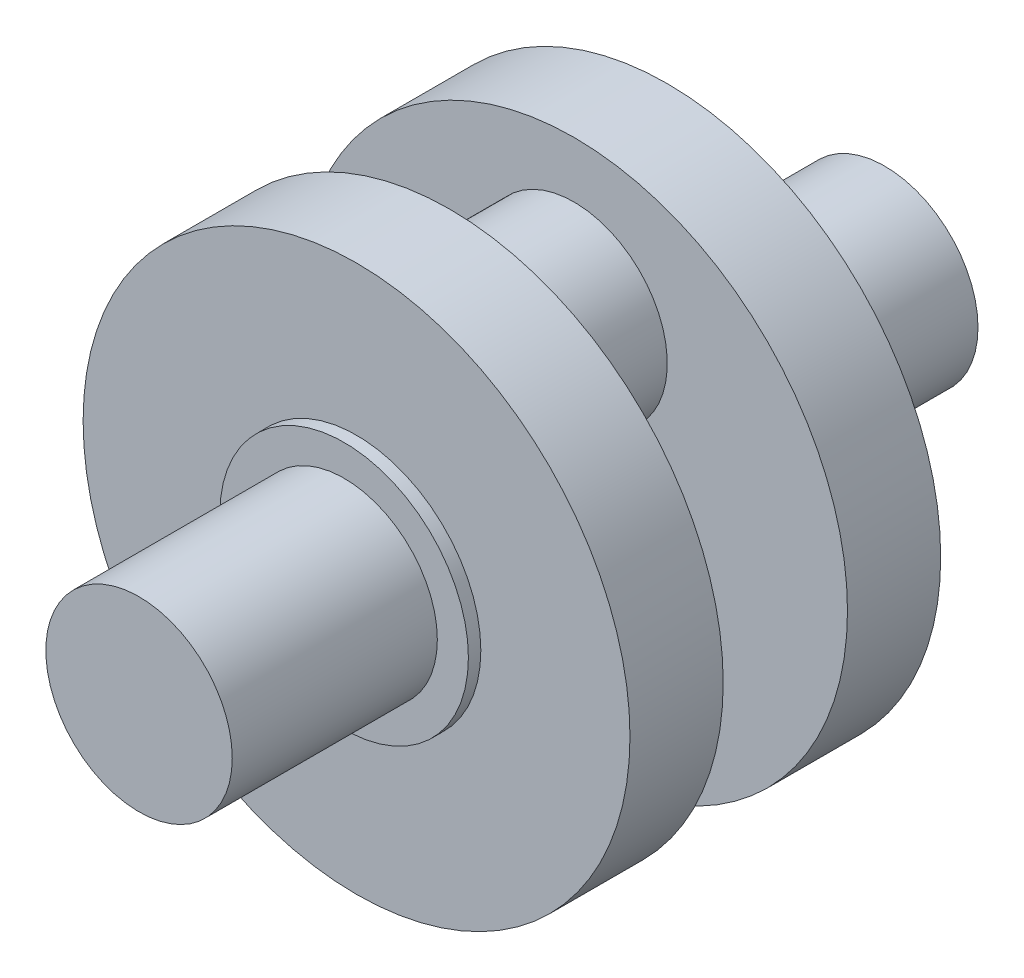
SolidWorks part; units mm, degrees
ref_plane "Płaszczyzna przednia" through (0, 0, 0) normal (0, 0, 1) x (1, 0, 0)
ref_plane "Płaszczyzna górna" through (0, 0, 0) normal (0, 1, 0) x (1, 0, 0)
ref_plane "Płaszczyzna prawa" through (0, 0, 0) normal (1, 0, 0) x (0, 0, -1)
sketch "Szkic1" plane through (0, 0, 0) normal (0, 0, 1) x (1, 0, 0)
  circle A0 centre (0, 0) radius 15
  dimension "D1" = 30
extrude "Dodanie-wyciągnięcie1" add sketch "Szkic1" along normal blind 33
sketch "Szkic2" plane through (0, 0, 0) normal (0, 0, -1) x (-1, 0, 0)
  circle A0 centre (0, 0) radius 20
  dimension "D1" = 40
extrude "Dodanie-wyciągnięcie2" add sketch "Szkic2" along normal blind 2
sketch "Szkic3" plane through (0, 0, -2) normal (0, 0, -1) x (-1, 0, 0)
  circle A0 centre (0, 0) radius 44
  dimension "D1" = 88
extrude "Dodanie-wyciągnięcie3" add sketch "Szkic3" along normal blind 15
sketch "Szkic4" plane through (0, 0, -17) normal (0, 0, -1) x (-1, 0, 0)
  circle A0 centre (0, 20) radius 15
  dimension "D2" = 30
  dimension "D1" = 20
extrude "Dodanie-wyciągnięcie4" add sketch "Szkic4" along normal blind 10
mirror "Lustro1" about plane through (0, 20, -27) normal (0, 0, -1) of bodies 104
